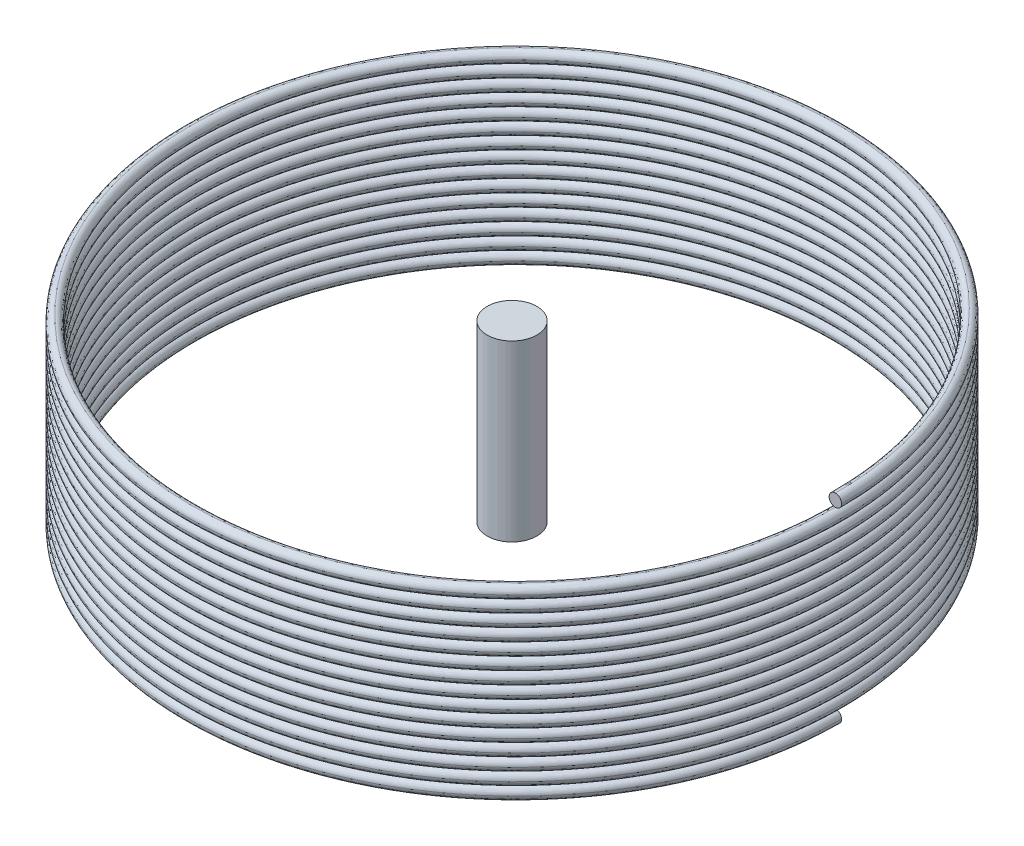
SolidWorks part; units mm, degrees
ref_plane "Plan de face" through (0, 0, 0) normal (0, 0, 1) x (1, 0, 0)
ref_plane "Plan de dessus" through (0, 0, 0) normal (0, 1, 0) x (1, 0, 0)
ref_plane "Plan de droite" through (0, 0, 0) normal (1, 0, 0) x (0, 0, -1)
sketch "Esquisse1" plane through (0, 0, 0) normal (0, 1, 0) x (1, 0, 0)
  circle A0 centre (0, 0) radius 13
curve "Hélice/Spirale1" pitch 0.5 height 7.5 turns 15
sketch "Esquisse2" plane through (0, 0, 0) normal (0, 0, 1) x (1, 0, 0)
  line L0 (0, 0) -> (0, 11.4483) construction
  line L1 (0, 0) -> (-13, 0) construction
  circle A0 centre (-13, 0) radius 0.25
sweep "Balayage1" add profiles "Esquisse2" path "Hélice/Spirale1"
sketch "Esquisse3" plane through (0, 0, 0) normal (0, 1, 0) x (1, 0, 0)
  circle A0 centre (0, 0) radius 1
extrude "Boss.-Extru.1" add sketch "Esquisse3" along normal blind 7 separate body
